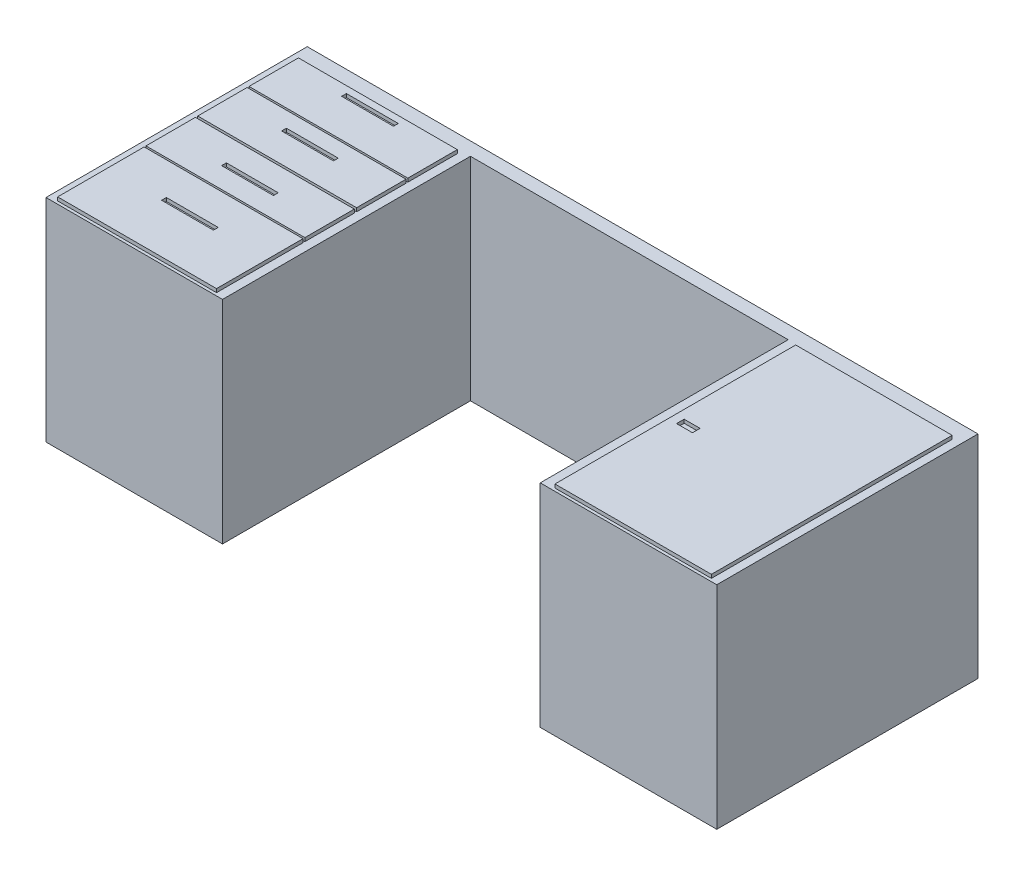
SolidWorks part; units mm, degrees
ref_plane "Front Plane" through (0, 0, 0) normal (0, 0, 1) x (1, 0, 0)
ref_plane "Top Plane" through (0, 0, 0) normal (0, 1, 0) x (1, 0, 0)
ref_plane "Right Plane" through (0, 0, 0) normal (1, 0, 0) x (0, 0, -1)
sketch "Sketch1" plane through (0, 0, 0) normal (0, 1, 0) x (1, 0, 0)
  line L0 (0, 0) -> (0, 740)
  line L1 (0, 740) -> (1900, 740)
  line L2 (1900, 740) -> (1900, 0)
  line L3 (1900, 0) -> (1400, 0)
  line L4 (1400, 0) -> (1400, 702.2632)
  line L5 (1400, 702.2632) -> (500, 702.2632)
  line L6 (500, 702.2632) -> (500, 0)
  line L7 (500, 0) -> (0, 0)
  dimension "D1" = 900
  dimension "D2" = 740
  dimension "D3" = 1900
  dimension "D4" = 500
extrude "Boss-Extrude1" add sketch "Sketch1" along normal blind 600 contours L1 L2 L3 L4 L5 L6 L7 L0
sketch "Sketch2" plane through (0, 600, 0) normal (0, 1, 0) x (1, 0, 0)
  line L0 (500, 702.2632) -> (500, 0) construction
  line L1 (25.0013, 690) -> (475.0013, 690)
  line L2 (25.0013, 690) -> (25.0013, 550)
  line L3 (25.0013, 550) -> (475.0013, 550)
  line L4 (475.0013, 690) -> (475.0013, 550)
  line L5 (25.0013, 544.7895) -> (475.0013, 544.7895)
  line L6 (25.0013, 544.7895) -> (25.0013, 404.7895)
  line L7 (25.0013, 404.7895) -> (475.0013, 404.7895)
  line L8 (475.0013, 544.7895) -> (475.0013, 404.7895)
  line L9 (25.0013, 398.2469) -> (475.0013, 398.2469)
  line L10 (25.0013, 398.2469) -> (25.0013, 258.2469)
  line L11 (25.0013, 258.2469) -> (475.0013, 258.2469)
  line L12 (475.0013, 398.2469) -> (475.0013, 258.2469)
  line L13 (25.0013, 253.0365) -> (475.0013, 253.0365)
  line L14 (0, 740) -> (1900, 740) construction
  line L15 (25.0013, 253.0365) -> (25.0013, 8.0365)
  line L16 (25.0013, 8.0365) -> (475.0013, 8.0365)
  line L17 (475.0013, 253.0365) -> (475.0013, 8.0365)
  line L18 (180.4489, 486.8982) -> (327.3623, 486.8982)
  line L19 (1876.8163, 8.0365) -> (1433.6113, 8.0365)
  line L20 (1876.8163, 8.0365) -> (1876.8163, 690)
  line L21 (1876.8163, 690) -> (1433.6113, 690)
  line L22 (1433.6113, 8.0365) -> (1433.6113, 690)
  line L23 (1457.7089, 328.4491) -> (1502.6979, 328.4491)
  line L24 (1457.7089, 328.4491) -> (1457.7089, 350)
  line L25 (1457.7089, 350) -> (1502.6979, 350)
  line L26 (1502.6979, 328.4491) -> (1502.6979, 350)
  line L27 (180.4489, 670.4799) -> (327.3623, 670.4799)
  line L28 (180.4489, 670.4799) -> (180.4489, 656.8982)
  line L29 (180.4489, 656.8982) -> (327.3623, 656.8982)
  line L30 (327.3623, 670.4799) -> (327.3623, 656.8982)
  line L31 (180.4489, 500.4799) -> (327.3623, 500.4799)
  line L32 (180.4489, 500.4799) -> (180.4489, 486.8982)
  line L33 (327.3623, 500.4799) -> (327.3623, 486.8982)
  line L34 (180.4489, 316.8982) -> (327.3623, 316.8982)
  line L35 (180.4489, 330.4799) -> (327.3623, 330.4799)
  line L36 (180.4489, 330.4799) -> (180.4489, 316.8982)
  line L37 (327.3623, 330.4799) -> (327.3623, 316.8982)
  line L38 (180.4489, 146.8982) -> (327.3623, 146.8982)
  line L39 (180.4489, 160.4799) -> (327.3623, 160.4799)
  line L40 (180.4489, 160.4799) -> (180.4489, 146.8982)
  line L41 (327.3623, 160.4799) -> (327.3623, 146.8982)
  dimension "D1" = 140
  dimension "D2" = 450
  dimension "D3" = 24.9987
  dimension "D4" = 5.2105
  dimension "D5" = 50
  dimension "D6" = 245
extrude "Boss-Extrude2" add sketch "Sketch2" along normal blind 10
